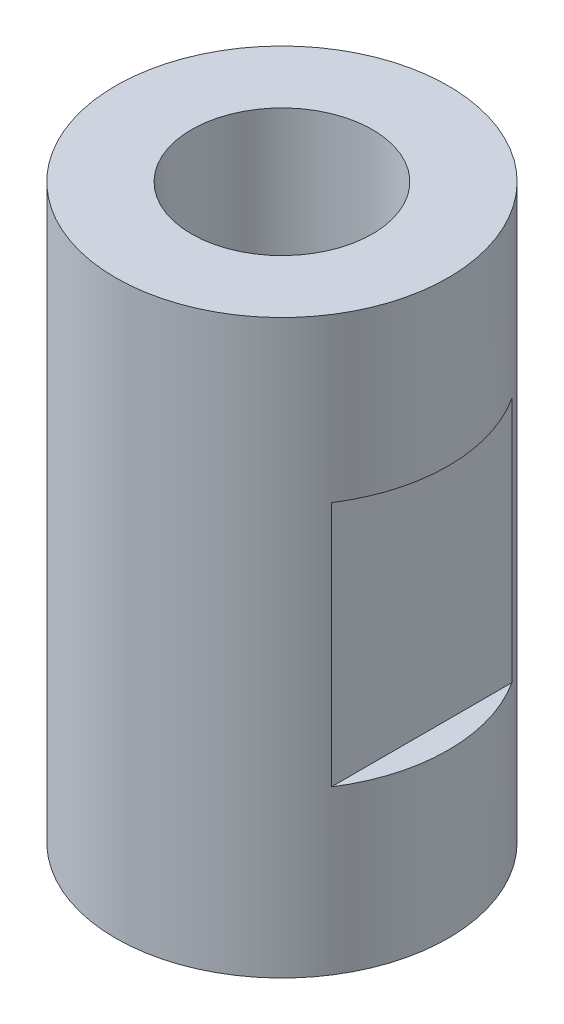
SolidWorks part; units mm, degrees
material "7075-T6 (SN)"
ref_plane "Front Plane" through (0, 0, 0) normal (0, 0, 1) x (1, 0, 0)
ref_plane "Top Plane" through (0, 0, 0) normal (0, 1, 0) x (1, 0, 0)
ref_plane "Right Plane" through (0, 0, 0) normal (1, 0, 0) x (0, 0, -1)
sketch "Sketch1" plane through (0, 0, 0) normal (0, 1, 0) x (1, 0, 0)
  circle A0 centre (0, 0) radius 6.35
  dimension "D1" = 12.7
extrude "Boss-Extrude1" add sketch "Sketch1" against normal blind 21.844
ref_plane "Plane1" through (0, 0, -6.35) normal (0, 0, -1) x (-1, 0, 0)
ref_plane "Plane2" through (0, 0, 6.35) normal (0, 0, 1) x (1, 0, 0)
sketch "Sketch4" plane through (0, 0, -6.35) normal (0, 0, -1) x (-1, 0, 0)
  line L0 (6.35, 0) -> (-6.35, 0) construction
  line L1 (-9.9641, -15.621) -> (-5.334, -15.621)
  line L2 (-9.9641, -15.621) -> (-9.9641, -6.223)
  line L3 (-9.9641, -6.223) -> (-5.334, -6.223)
  line L4 (-5.334, -15.621) -> (-5.334, -6.223)
  line L5 (5.334, -6.223) -> (10.9184, -6.223)
  line L6 (5.334, -6.223) -> (5.334, -15.621)
  line L7 (5.334, -15.621) -> (10.9184, -15.621)
  line L8 (10.9184, -6.223) -> (10.9184, -15.621)
  dimension "D1" = 5.334
  dimension "D2" = 5.334
  dimension "D3" = 10.668
  dimension "D4" = 6.223
  dimension "D5" = 9.398
  dimension "D6" = 6.223
extrude "Cut-Extrude5" cut sketch "Sketch4" against normal through all
sketch "Sketch6" plane through (0, 0, 0) normal (0, 1, 0) x (1, 0, 0)
  point P0 (0, 0)
hole_wizard "M5x0.8 Tapped Hole2" positions "Sketch7" profile "Sketch8" tap size "M5x0.8" standard "ANSI Metric" end condition through all
sketch "Sketch7" plane through (0, 0, 0) normal (0, 1, 0) x (1, 0, 0)
  point P0 (0, 0)
cosmetic thread "Hole Thread1" parameters "D2"=5
sketch "Sketch8" plane through (0, 0, 0) normal (1, 0, 0) x (0, 0, 1)
  line L0 (0, 0) -> (0, 21.844)
  line L1 (0, 21.844) -> (2.1, 21.844)
  line L2 (2.1, 21.844) -> (2.1, 0)
  line L5 (2.1, 0) -> (0, 0)
  line L11 (0, -6.35) -> (0, 107.95) construction
  dimension "Thru Tap Drill Dia." = 4.2
  dimension "Thru Tap Drill Depth" = 21.844
hole_wizard "5/16-24 Tapped Hole1" positions "Sketch9" profile "Sketch11" tap size "5/16-24" standard "ANSI Inch"
sketch "Sketch9" plane through (0, 0, 0) normal (0, 1, 0) x (1, 0, 0)
  point P0 (0, 0)
sketch "Sketch11" plane through (0, 0, 0) normal (1, 0, 0) x (0, 0, 1)
  line L0 (0, 0) -> (0, 8.4256)
  line L1 (0, 8.4256) -> (3.4544, 6.35)
  line L2 (3.4544, 6.35) -> (3.4544, 0)
  line L5 (3.4544, 0) -> (0, 0)
  line L10 (0, 8.4256) -> (-3.4544, 6.35) construction
  line L11 (0, -6.35) -> (0, 107.95) construction
  dimension "Tap Drill Dia." = 6.9088
  dimension "Tap Drill Depth" = 6.35
  dimension "Drill Angle" = 118
cosmetic thread "Hole Thread2" parameters "D1"=9.906, "D2"=8.8176
